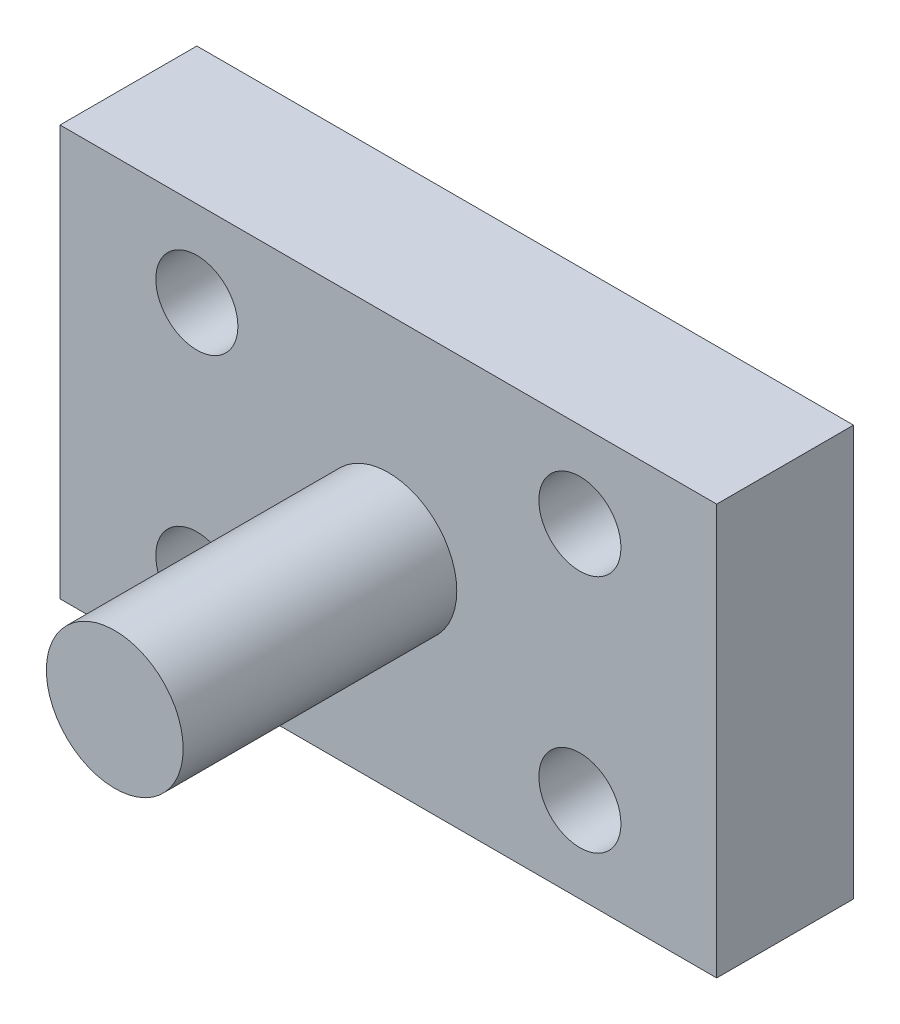
SolidWorks part; units mm, degrees
ref_plane "前视基准面" through (0, 0, 0) normal (0, 0, 1) x (1, 0, 0)
ref_plane "上视基准面" through (0, 0, 0) normal (0, 1, 0) x (1, 0, 0)
ref_plane "右视基准面" through (0, 0, 0) normal (1, 0, 0) x (0, 0, -1)
sketch "Sketch1" plane through (0, 0, 0) normal (0, 0, 1) x (1, 0, 0)
  line L1 (-60, 37.5) -> (60, 37.5)
  line L2 (-60, 37.5) -> (-60, -37.5)
  line L3 (-60, -37.5) -> (60, -37.5)
  line L4 (60, 37.5) -> (60, -37.5)
  line L5 (-60, 37.5) -> (60, -37.5) construction
  line L6 (-60, -37.5) -> (60, 37.5) construction
  circle A0 centre (35, 21.875) radius 7.5
  circle A1 centre (-35, 21.875) radius 7.5
  circle A2 centre (-35, -21.875) radius 7.5
  circle A3 centre (35, -21.875) radius 7.5
  point P0 (0, 0)
  point P14 (-166.476, 87.6747)
  point P16 (-31.5727, 37.5)
  point P17 (-36.063, 37.5)
  point P18 (-22.8727, 37.5)
  point P19 (-24.5565, -37.5)
  dimension "D1" = 15
  dimension "D2" = 120
  dimension "D3" = 75
  dimension "D4" = 25
  dimension "D5" = 25
  dimension "D6" = 25
  dimension "D7" = 25
extrude "Boss-Extrude1" add sketch "Sketch1" along normal blind 25
sketch "Sketch2" plane through (0, 0, 25) normal (0, 0, 1) x (1, 0, 0)
  circle A0 centre (0, 0) radius 12.5
  dimension "D1" = 25
extrude "Boss-Extrude2" add sketch "Sketch2" along normal blind 50
